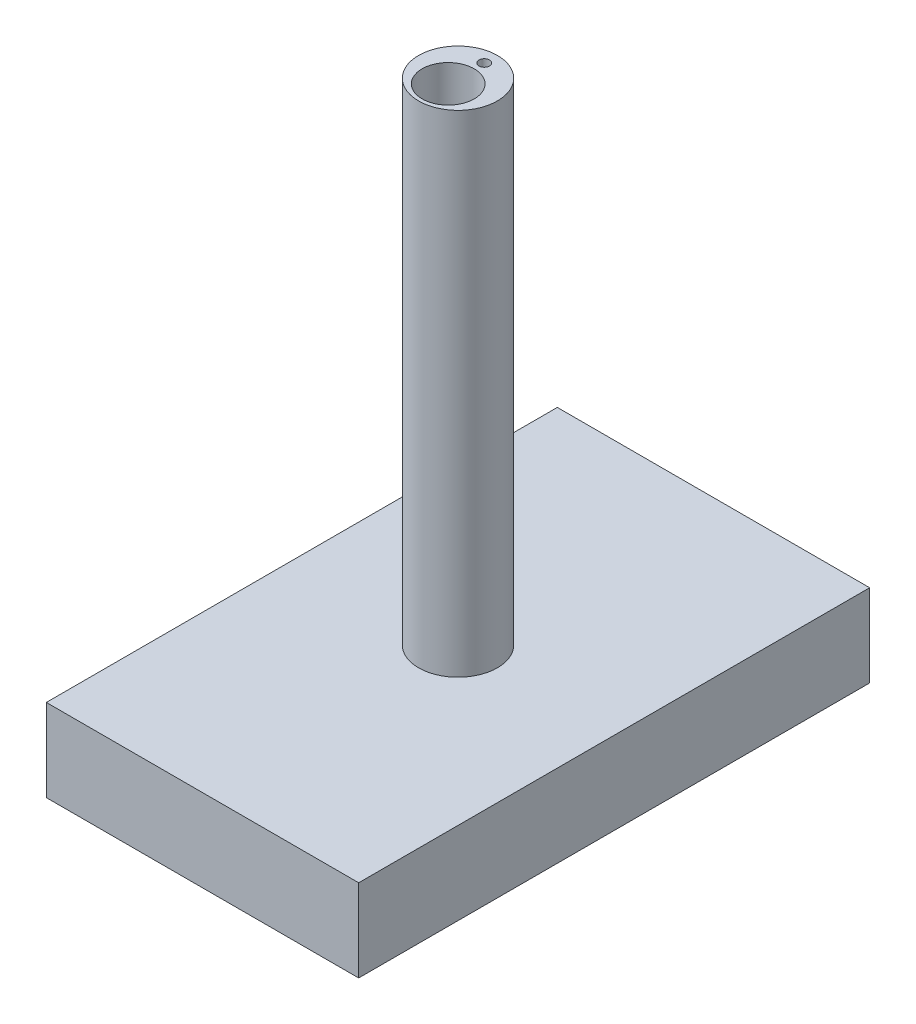
SolidWorks part; units mm, degrees
ref_plane "Front Plane" through (0, 0, 0) normal (0, 0, 1) x (1, 0, 0)
ref_plane "Top Plane" through (0, 0, 0) normal (0, 1, 0) x (1, 0, 0)
ref_plane "Right Plane" through (0, 0, 0) normal (1, 0, 0) x (0, 0, -1)
sketch "Sketch1" plane through (0, 0, 0) normal (0, 1, 0) x (1, 0, 0)
  circle A0 centre (0, 0) radius 28.1
extrude "Boss-Extrude1" add sketch "Sketch1" along normal blind 350
sketch "Sketch2" plane through (0, 350, 0) normal (0, 1, 0) x (1, 0, 0)
  circle A0 centre (0, -7) radius 18.6
extrude "Cut-Extrude1" cut sketch "Sketch2" against normal blind 58.8
sketch "Sketch3" plane through (0, 0, 0) normal (0, -1, 0) x (-1, 0, 0)
  line L1 (111.3415, -182.1414) -> (-111.3415, -182.1414)
  line L2 (111.3415, -182.1414) -> (111.3415, 182.1414)
  line L3 (111.3415, 182.1414) -> (-111.3415, 182.1414)
  line L4 (-111.3415, -182.1414) -> (-111.3415, 182.1414)
  line L5 (111.3415, -182.1414) -> (-111.3415, 182.1414) construction
  line L6 (111.3415, 182.1414) -> (-111.3415, -182.1414) construction
  point P0 (0, 0)
extrude "Boss-Extrude2" add sketch "Sketch3" along normal blind 58.8
sketch "Sketch4" plane through (0, -58.8, 0) normal (0, -1, 0) x (-1, 0, 0)
  line L1 (103.9587, -174.2721) -> (-103.9587, -174.2721)
  line L2 (103.9587, -174.2721) -> (103.9587, 174.2721)
  line L3 (103.9587, 174.2721) -> (-103.9587, 174.2721)
  line L4 (-103.9587, -174.2721) -> (-103.9587, 174.2721)
  line L5 (103.9587, -174.2721) -> (-103.9587, 174.2721) construction
  line L6 (103.9587, 174.2721) -> (-103.9587, -174.2721) construction
  point P0 (0, 0)
extrude "Cut-Extrude2" cut sketch "Sketch4" against normal blind 48.8
sketch "Sketch5" plane through (0, 291.2, 0) normal (0, 1, 0) x (1, 0, 0)
  circle A1 centre (0, -7) radius 16.1
extrude "Cut-Extrude3" cut sketch "Sketch5" against normal blind 350
sketch "Sketch6" plane through (0, 350, 0) normal (0, 1, 0) x (1, 0, 0)
  circle A1 centre (0, 18.75) radius 3.75
extrude "Cut-Extrude5" cut sketch "Sketch6" against normal blind 400
sketch "Sketch7" plane through (0, -10, 0) normal (0, -1, 0) x (-1, 0, 0)
  line L0 (-33, 69.19) -> (-30.5, 69.19)
  line L2 (30.5, 109.19) -> (33, 109.19)
  line L15 (33, 109.19) -> (33, 149.19)
  line L16 (-33, 149.19) -> (-33, 69.19)
  line L17 (-30.5, 69.19) -> (-30.5, 146.69)
  line L18 (30.5, 146.69) -> (30.5, 109.19)
  line L19 (30.5, 146.69) -> (-30.5, 146.69)
  line L20 (33, 149.19) -> (-33, 149.19)
  point P5 (0, 109.19)
  point P10 (0, 109.19)
extrude "Boss-Extrude3" add sketch "Sketch7" along normal blind 10
sketch "Sketch8" plane through (0, 0, -182.1414) normal (0, 0, -1) x (-1, 0, 0)
  circle A0 centre (-86.5737, -25.0112) radius 10
extrude "Cut-Extrude7" cut sketch "Sketch8" against normal blind 10 contours A0
sketch "Sketch9" plane through (-30.5, 0, 0) normal (1, 0, 0) x (0, 0, -1)
  line L0 (109.19, -20) -> (109.19, -10) construction
  line L1 (146.69, -20) -> (109.19, -20)
  line L2 (146.69, -20) -> (146.69, -19)
  line L3 (146.69, -19) -> (109.19, -19)
  line L4 (109.19, -20) -> (109.19, -19)
extrude "Boss-Extrude4" add sketch "Sketch9" along normal blind 1
sketch "Sketch10" plane through (-30.5, 0, 0) normal (1, 0, 0) x (0, 0, -1)
  line L1 (109.19, -19) -> (109.19, -10) construction
  line L2 (146.69, -19) -> (146.69, -10) construction
  line L3 (109.19, -15) -> (146.69, -15)
  line L4 (109.19, -15) -> (109.19, -14)
  line L5 (109.19, -14) -> (146.69, -14)
  line L6 (146.69, -15) -> (146.69, -14)
extrude "Boss-Extrude5" add sketch "Sketch10" along normal blind 1
sketch "Sketch11" plane through (30.5, 0, 0) normal (-1, 0, 0) x (0, 0, 1)
  line L0 (-69.19, -20) -> (-69.19, -10) construction
  line L1 (-146.69, -20) -> (-69.19, -20)
  line L2 (-146.69, -20) -> (-146.69, -19)
  line L3 (-146.69, -19) -> (-69.19, -19)
  line L4 (-69.19, -20) -> (-69.19, -19)
extrude "Boss-Extrude6" add sketch "Sketch11" along normal blind 1
sketch "Sketch12" plane through (30.5, 0, 0) normal (-1, 0, 0) x (0, 0, 1)
  line L1 (-69.19, -19) -> (-69.19, -10) construction
  line L2 (-146.69, -19) -> (-146.69, -10) construction
  line L3 (-69.19, -15) -> (-146.69, -15)
  line L4 (-69.19, -15) -> (-69.19, -14)
  line L5 (-69.19, -14) -> (-146.69, -14)
  line L6 (-146.69, -15) -> (-146.69, -14)
extrude "Boss-Extrude7" add sketch "Sketch12" along normal blind 1
